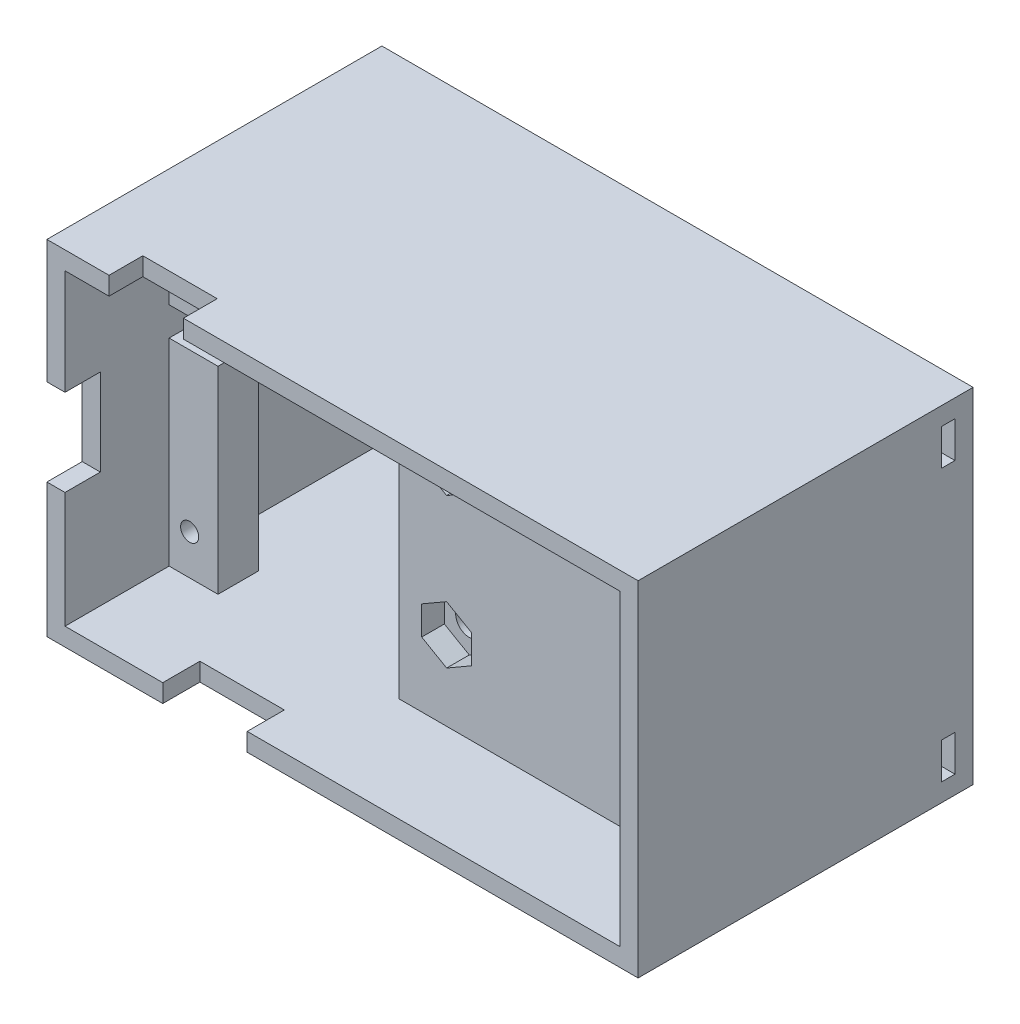
SolidWorks part; units mm, degrees
other "标注1"
sketch "草图16" plane through (3.3763, -43.0665, -26) normal (0.531, -0.7584, -0.3779) x (-0.8474, -0.4776, -0.2321)
other "标注2"
sketch "草图17" plane through (-61.9234, -43.0665, 5.5) normal (-0.5977, -0.3514, 0.7206) x (0.795, -0.3761, 0.4759)
ref_plane "前视基准面" through (0, 0, 0) normal (0, 0, 1) x (1, 0, 0)
ref_plane "上视基准面" through (0, 0, 0) normal (0, 1, 0) x (1, 0, 0)
ref_plane "右视基准面" through (0, 0, 0) normal (1, 0, 0) x (0, 0, -1)
ref_plane "基准面1" through (0, 0, 3.6001) normal (0, 0, 1) x (1, 0, 0)
sketch "草图1" plane through (0, 0, 3.6001) normal (0, 0, 1) x (1, 0, 0)
  line L0 (0.8763, -38.7224) -> (-59.4234, -38.7224) construction
  line L1 (-48.7034, -33.8618) -> (-39.801, -33.8618)
  line L2 (-48.7034, -33.8618) -> (-48.7034, -38.7224)
  line L4 (-39.801, -33.8618) -> (-39.801, -38.7224)
  line L5 (-59.4234, -9.4107) -> (0.8763, -9.4107) construction
  line L7 (-55.7687, -9.4107) -> (-55.7687, -14.2907)
  line L8 (-55.7687, -14.2907) -> (-45.8066, -14.2907)
  line L9 (-45.8066, -9.4107) -> (-45.8066, -14.2907)
  line L10 (-12.699, -17.609) -> (-12.699, -12.109) construction
  line L11 (0.8763, -9.4107) -> (-45.8066, -9.4107)
  line L12 (0.8763, -9.4107) -> (0.8763, -38.7224)
  line L13 (0.8763, -38.7224) -> (-39.801, -38.7224)
  line L14 (-59.4234, -9.4107) -> (-59.4234, -19.2521)
  line L15 (-29.2736, -33.0846) -> (-20.6538, -33.0846)
  line L16 (-29.2736, -33.0846) -> (-29.2736, -36.2921)
  line L17 (-29.2736, -36.2921) -> (-20.6538, -36.2921)
  line L18 (-20.6538, -33.0846) -> (-20.6538, -36.2921)
  line L23 (-12.699, -12.109) -> (-9.399, -12.109)
  line L24 (-12.699, -12.109) -> (-12.699, -17.609)
  line L25 (-12.699, -17.609) -> (-9.399, -17.609)
  line L26 (-9.399, -12.109) -> (-9.399, -17.609)
  line L27 (-48.7034, -38.7224) -> (-59.4234, -38.7224)
  line L28 (-55.7687, -9.4107) -> (-59.4234, -9.4107)
  line L29 (-59.4234, -27.6866) -> (-59.4234, -38.7224)
  line L30 (-59.4234, -19.2521) -> (-54.3557, -19.2521)
  line L32 (-59.4234, -27.6866) -> (-54.3557, -27.6866)
  line L33 (-54.3557, -19.2521) -> (-54.3557, -27.6866)
  circle A0 centre (-57.6581, -36.6498) radius 1
  circle A1 centre (-57.6581, -11.2498) radius 1
  circle A2 centre (-1.016, -11.2498) radius 1
  circle A3 centre (-0.889, -36.8301) radius 1
  circle A4 centre (-4.1259, -29.4689) radius 1.322
  circle A5 centre (-5.9082, -27.2775) radius 0.4462
  circle A6 centre (-4.5737, -26.6799) radius 0.4462
  circle A7 centre (-3.1192, -26.8297) radius 0.4462
  circle A8 centre (-1.9345, -27.6866) radius 0.4462
  circle A9 centre (-1.3369, -29.0211) radius 0.4462
  circle A10 centre (-1.4866, -30.4756) radius 0.4462
  circle A11 centre (-2.3435, -31.6603) radius 0.4462
  circle A12 centre (-3.678, -32.2579) radius 0.4462
  circle A13 centre (-5.1325, -32.1082) radius 0.4462
  circle A14 centre (-6.3173, -31.2513) radius 0.4462
  circle A15 centre (-6.9149, -29.9168) radius 0.4462
  circle A16 centre (-6.7652, -28.4623) radius 0.4462
  point P71 (-4.1259, -29.4689)
  dimension "D1" = 12
ref_plane "基准面2" through (0, 0, -6) normal (0, 0, -1) x (-1, 0, 0)
sketch "草图2" plane through (0, 0, -6) normal (0, 0, -1) x (-1, 0, 0)
  line L0 (29.2736, -9.4107) -> (29.2736, -38.7224) construction
  line L1 (-0.8763, -38.7224) -> (59.4234, -38.7224)
  line L2 (-0.8763, -38.7224) -> (-0.8763, -9.4107)
  line L3 (-0.8763, -9.4107) -> (59.4234, -9.4107)
  line L4 (59.4234, -38.7224) -> (59.4234, -9.4107)
  line L5 (59.4234, -24.0665) -> (-9.3078, -24.0665) construction
  line L6 (-3.3763, -5.0665) -> (61.9234, -43.0665) construction
  line L9 (29.2736, -15.8165) -> (29.2736, -13.1836) construction
  line L10 (27.7854, -15.8165) -> (27.7854, -13.1836)
  line L11 (30.7617, -15.8165) -> (30.7617, -13.1836)
  line L12 (29.2736, -38.7224) -> (29.2736, -43.3487) construction
  line L13 (-3.3763, -43.0665) -> (61.9234, -5.0665) construction
  line L14 (-3.3763, -5.0665) -> (61.9234, -5.0665)
  line L15 (-3.3763, -5.0665) -> (-3.3763, -43.0665)
  line L16 (-3.3763, -43.0665) -> (61.9234, -43.0665)
  line L17 (61.9234, -5.0665) -> (61.9234, -43.0665)
  circle A0 centre (1.016, -11.2498) radius 1
  circle A1 centre (0.889, -36.8301) radius 1
  circle A2 centre (57.6581, -36.6498) radius 1
  circle A3 centre (57.6581, -11.2498) radius 0.9222
  arc A10 (27.7854, -15.8165) -> (30.7617, -15.8165) centre (29.2736, -15.8165) ccw
  arc A11 (30.7617, -13.1836) -> (27.7854, -13.1836) centre (29.2736, -13.1836) ccw
  circle A12 centre (29.2736, -32.3165) radius 1.5
  point P24 (29.2736, -24.0665)
  point P27 (29.2736, -31.5665)
  point P28 (29.2736, -24.0665)
  point P29 (0, 0)
  point P30 (29.2736, -3.8958)
  point P33 (29.2736, -14.5001)
  dimension "D1" = 38
  dimension "D2" = 2.5
  dimension "D3" = 3
  dimension "D4" = 8.25
  dimension "D5" = 2.5
  dimension "D7" = 8.25
extrude "凸台-拉伸2" add sketch "草图2" along normal blind 4.5 separate body
sketch "草图3" plane through (0, 0, -6) normal (0, 0, -1) x (-1, 0, 0)
  line L0 (29.2736, -15.8165) -> (29.2736, -10.8487) construction
  line L1 (32.0236, -17.4043) -> (32.0236, -14.2288)
  line L4 (26.5236, -14.2288) -> (26.5236, -17.4043)
  line L5 (26.5236, -17.4043) -> (29.2736, -18.992)
  line L6 (29.2736, -18.992) -> (32.0236, -17.4043)
  line L8 (32.0236, -14.9203) -> (32.0236, -11.7449)
  line L9 (32.0236, -11.7449) -> (29.2736, -10.1572)
  line L10 (29.2736, -10.1572) -> (26.5236, -11.7449)
  line L11 (26.5236, -11.7449) -> (26.5236, -14.9203)
  line L14 (31.8974, -14.9932) -> (32.0236, -14.9203) [skipped]
  line L15 (29.2736, -22.4541) -> (17.663, -22.4541) construction
  line L16 (29.2736, -22.4541) -> (29.2736, -17.3047) construction
  line L17 (26.6497, -14.156) -> (26.5236, -14.2288) [skipped]
  line L18 (26.5236, -14.9203) -> (26.6497, -14.9932) [skipped]
  line L19 (32.0236, -14.2288) -> (31.8974, -14.156) [skipped]
  line L20 (26.5236, -33.9043) -> (29.2736, -35.492)
  line L21 (29.2736, -35.492) -> (32.0236, -33.9043)
  line L22 (32.0236, -33.9043) -> (32.0236, -30.7288)
  line L23 (32.0236, -30.7288) -> (29.2736, -29.1411)
  line L24 (29.2736, -29.1411) -> (26.5236, -30.7288)
  line L25 (26.5236, -30.7288) -> (26.5236, -33.9043)
  arc A0 (26.82, -14.5746) -> (31.7271, -14.5746) centre (29.2736, -15.8165) ccw construction
  arc A1 (31.7271, -14.5746) -> (26.82, -14.5746) centre (29.2736, -13.3326) ccw construction
  circle A2 centre (29.2736, -32.3165) radius 2.75 construction
  circle A3 centre (1.016, -11.2498) radius 1.75
  circle A4 centre (57.6581, -11.2498) radius 1.75
  arc A5 (27.7854, -15.8165) -> (30.7617, -15.8165) centre (29.2736, -15.8165) ccw construction
  circle A6 centre (0.889, -36.8301) radius 1.75
  circle A7 centre (57.6581, -36.6498) radius 1.75
  point P25 (29.2736, -33.8241)
  dimension "D2" = 3.5
  dimension "D1" = 5.5
extrude "切除-拉伸2" cut sketch "草图3" along normal blind 2.5 contours L10 L11 L4 L5 L6 L1 L8 L9 | L24 L25 L20 L21 L22 L23
sketch "草图5" plane through (0, 0, -10.5) normal (0, 0, -1) x (-1, 0, 0)
  line L0 (29.2736, -7.0665) -> (29.2736, -48.0798) construction
  line L5 (-1.3763, -7.0665) -> (59.9234, -7.0665)
  line L6 (-1.3763, -7.0665) -> (-1.3763, -41.0665)
  line L7 (-1.3763, -41.0665) -> (59.9234, -41.0665)
  line L8 (59.9234, -7.0665) -> (59.9234, -41.0665)
  line L9 (-3.3763, -5.0665) -> (61.9234, -5.0665)
  line L10 (-3.3763, -5.0665) -> (-3.3763, -43.0665)
  line L11 (-3.3763, -43.0665) -> (61.9234, -43.0665)
  line L12 (61.9234, -5.0665) -> (61.9234, -43.0665)
  line L13 (-0.8763, -9.4107) -> (59.4234, -38.7224) construction
  line L14 (-1.3763, -7.0665) -> (59.9234, -41.0665) construction
  line L15 (-3.3763, -5.0665) -> (61.9234, -43.0665) construction
  line L16 (61.9234, -5.0665) -> (-3.3763, -43.0665) construction
  point P12 (29.2736, -24.0665)
  point P13 (29.2736, -24.0665)
  point P18 (29.2736, -24.0665)
  point P19 (0, 0)
  dimension "D1" = 61.2997
  dimension "D2" = 38
  dimension "D3" = 34
  dimension "D4" = 2
extrude "凸台-拉伸3" add sketch "草图5" along normal blind 21 and the other way blind 16
sketch "草图7" plane through (0, -5.0665, 0) normal (0, 1, 0) x (1, 0, 0)
  line L0 (-41.7981, -5.5601) -> (-46.8481, -5.5601) construction
  line L1 (-55.0622, -1.765) -> (-46.8481, -1.765)
  line L2 (-55.0622, -1.765) -> (-55.0622, -5.5601)
  line L3 (-55.0622, -5.5601) -> (-46.8481, -5.5601)
  line L4 (-46.8481, -1.765) -> (-46.8481, -5.5601)
extrude "切除-拉伸4" cut sketch "草图7" against normal blind 3
sketch "草图8" plane through (-61.9234, 0, 0) normal (-1, 0, 0) x (0, 0, 1)
  line L0 (5.6001, -27.6866) -> (5.6001, -38.7224) construction
  line L1 (1.6001, -18.6953) -> (5.6001, -18.6953)
  line L2 (1.6001, -18.6953) -> (1.6001, -28.2708)
  line L3 (1.6001, -28.2708) -> (5.6001, -28.2708)
  line L4 (5.6001, -18.6953) -> (5.6001, -28.2708)
  dimension "D1" = 4
extrude "切除-拉伸5" cut sketch "草图8" against normal blind 3
sketch "草图9" plane through (0, -43.0665, 0) normal (0, -1, 0) x (1, 0, 0)
  line L0 (-59.4234, 5.6001) -> (-48.7034, 5.6001) construction
  line L1 (-49.1273, 5.6001) -> (-39.801, 5.6001)
  line L2 (-49.1273, 5.6001) -> (-49.1273, 1.3978)
  line L3 (-49.1273, 1.3978) -> (-39.801, 1.3978)
  line L4 (-39.801, 5.6001) -> (-39.801, 1.3978)
extrude "切除-拉伸6" cut sketch "草图9" against normal blind 3
sketch "草图13" plane through (0, 0, -6) normal (0, 0, 1) x (1, 0, 0)
  line L2 (-59.9234, -16.0665) -> (-59.9234, -19.2521)
  line L3 (-59.9234, -19.2521) -> (-54.5253, -19.2521)
  line L5 (-59.9234, -16.0665) -> (-54.5253, -16.0665)
  line L6 (-49.1273, -41.0665) -> (-59.9234, -41.0665) construction
  line L7 (-54.5253, -41.0665) -> (-34.5253, -41.0665)
  line L8 (-54.5253, -41.0665) -> (-54.5253, -19.2521)
  line L9 (-54.5253, -7.0665) -> (-34.5253, -7.0665)
  line L10 (-34.5253, -41.0665) -> (-34.5253, -7.0665)
  line L11 (-46.8481, -7.0665) -> (1.3763, -7.0665) construction
  line L12 (-54.5253, -16.0665) -> (-54.5253, -12.8809)
  line L13 (-54.5253, -12.8809) -> (-54.5253, -7.0665)
  dimension "D2" = 20
extrude "切除-拉伸7" cut sketch "草图13" against normal blind 10
sketch "草图15" plane through (0, 0, -10.5) normal (0, 0, -1) x (-1, 0, 0)
  circle A0 centre (1.016, -11.2498) radius 1.75
  circle A1 centre (57.6581, -11.2498) radius 1.75
  circle A2 centre (0.889, -36.8301) radius 1.75
  circle A3 centre (57.6581, -36.6498) radius 1.75
  dimension "D1" = 3.5
extrude "切除-拉伸8" cut sketch "草图15" against normal blind 1.5
sketch "草图18" plane through (0, 0, -31.5) normal (0, 0, -1) x (-1, 0, 0)
  line L0 (59.9234, -7.0665) -> (-1.3763, -7.0665) construction
  line L1 (-1.3763, -6.5665) -> (59.9234, -6.5665)
  line L2 (-1.3763, -6.5665) -> (-1.3763, -41.5665)
  line L3 (-1.3763, -41.5665) -> (59.9234, -41.5665)
  line L4 (59.9234, -6.5665) -> (59.9234, -41.5665)
  line L5 (-1.3763, -41.0665) -> (34.5253, -41.0665) construction
  dimension "D1" = 0.5
  dimension "D2" = 0.5
extrude "切除-拉伸9" cut sketch "草图18" against normal blind 2
sketch "草图19" plane through (1.3763, 0, 0) normal (-1, 0, 0) x (0, 0, 1)
  line L0 (-31.5, -43.0665) -> (-31.5, -5.0665) construction
  line L1 (-29.5, -7.0665) -> (-28, -7.0665)
  line L2 (-29.5, -7.0665) -> (-29.5, -11.0665)
  line L3 (-29.5, -11.0665) -> (-28, -11.0665)
  line L4 (-28, -7.0665) -> (-28, -11.0665)
  line L5 (-31.5, -5.0665) -> (5.5, -5.0665) construction
  line L6 (-31.5, -24.0665) -> (15.6063, -24.0665) construction
  line L7 (-29.5, -37.0665) -> (-28, -37.0665)
  line L8 (-28, -41.0665) -> (-28, -37.0665)
  line L9 (-29.5, -41.0665) -> (-28, -41.0665)
  line L10 (-29.5, -41.0665) -> (-29.5, -37.0665)
  dimension "D1" = 2
  dimension "D2" = 1.5
  dimension "D3" = 2
  dimension "D4" = 4
extrude "切除-拉伸10" cut sketch "草图19" against normal blind 2
